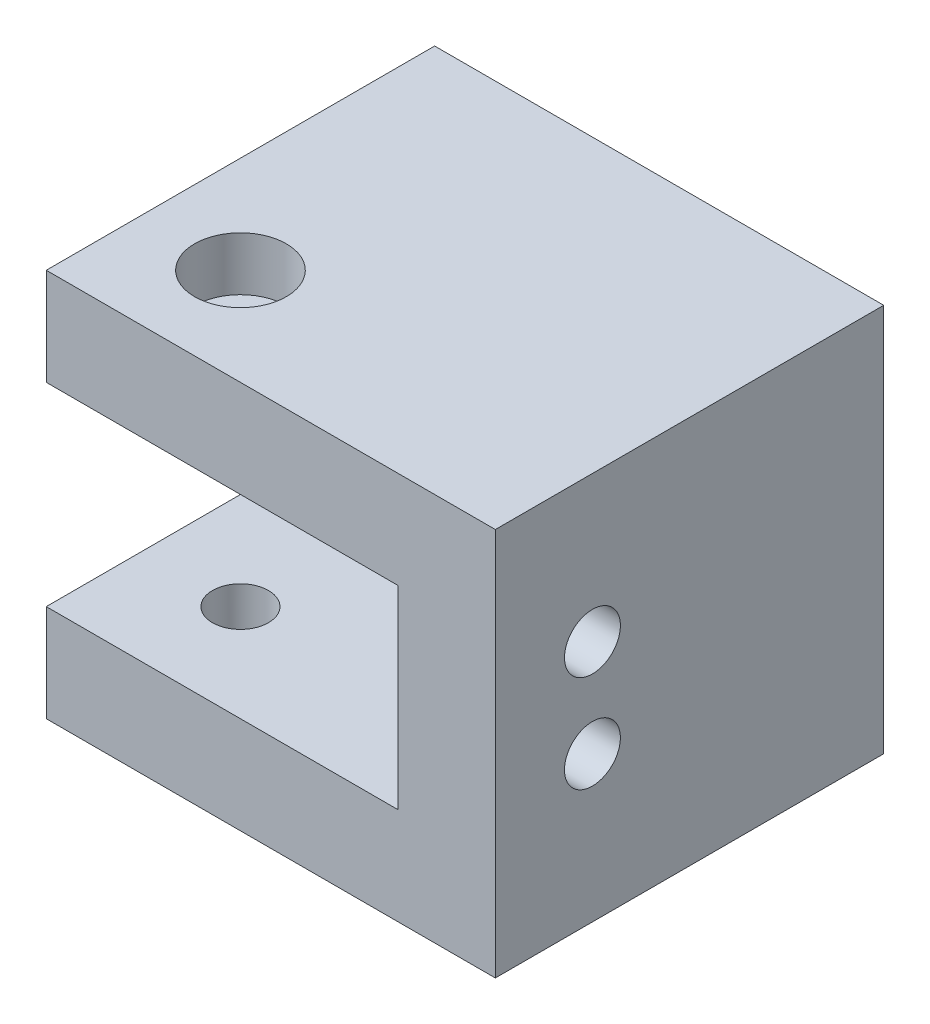
SolidWorks part; units mm, degrees
material "6061 Alloy"
ref_plane "Front Plane" through (0, 0, 0) normal (0, 0, 1) x (1, 0, 0)
ref_plane "Top Plane" through (0, 0, 0) normal (0, 1, 0) x (1, 0, 0)
ref_plane "Right Plane" through (0, 0, 0) normal (1, 0, 0) x (0, 0, -1)
sketch "Sketch1" plane through (0, 0, 0) normal (0, 0, 1) x (1, 0, 0)
  line L1 (0, 0) -> (29.3688, 0)
  line L2 (0, 0) -> (0, 25.4)
  line L3 (0, 25.4) -> (29.3687, 25.4)
  line L4 (29.3688, 0) -> (29.3687, 25.4)
  dimension "D1" = 29.3688
  dimension "D2" = 25.4
extrude "Boss-Extrude1" add sketch "Sketch1" along normal blind 25.4
sketch "Sketch2" plane through (0, 0, 25.4) normal (0, 0, 1) x (1, 0, 0)
  line L0 (0, 25.4) -> (0, 0) construction
  line L1 (0, 19.05) -> (23.0188, 19.05)
  line L2 (0, 19.05) -> (0, 6.35)
  line L3 (0, 6.35) -> (23.0188, 6.35)
  line L4 (23.0188, 19.05) -> (23.0188, 6.35)
  line L5 (29.3688, 0) -> (29.3688, 25.4) construction
  line L6 (29.3687, 25.4) -> (0, 25.4) construction
  line L7 (0, 0) -> (29.3688, 0) construction
  dimension "D1" = 6.35
  dimension "D2" = 6.35
  dimension "D3" = 6.35
extrude "Cut-Extrude1" cut sketch "Sketch2" against normal blind 15.875
hole_wizard "CBORE for #6 Socket Head Cap Screw1" positions "Sketch4" profile "Sketch5" counterbore size "#6" standard "ANSI Inch" end condition through all
sketch "Sketch4" plane through (0, 25.4, 0) normal (0, 1, 0) x (1, 0, 0)
  line L0 (0, -25.4) -> (0, 0) construction
  line L1 (29.3687, -25.4) -> (0, -25.4) construction
  point P0 (6.35, -19.05)
  dimension "D1" = 6.35
  dimension "D2" = 6.35
sketch "Sketch5" plane through (6.35, 25.4, 19.05) normal (1, 0, 0) x (0, 0, 1)
  line L0 (0, 0) -> (0, 25.4)
  line L1 (0, 25.4) -> (1.8288, 25.4)
  line L3 (1.8288, 25.4) -> (1.8288, 3.5052)
  line L4 (1.8288, 3.5052) -> (3, 3.5052)
  line L5 (3, 3.5052) -> (3, 0)
  line L7 (3, 0) -> (0, 0)
  line L11 (0, -6.35) -> (0, 107.95) construction
  dimension "Thru Hole Dia." = 3.6576
  dimension "Thru Hole Depth" = 25.4
  dimension "C'Bore Dia." = 6
  dimension "C'Bore Depth" = 3.5052
hole_wizard "#6 Clearance Hole2" positions "Sketch7" profile "Sketch6" hole size "#6" standard "ANSI Inch" end condition through all
sketch "Sketch7" plane through (29.3688, 0, 0) normal (1, 0, 0) x (0, 0, -1)
  line L0 (-25.4, 0) -> (-25.4, 25.4) construction
  line L1 (-25.4, 25.4) -> (0, 25.4) construction
  line L2 (-25.4, 0) -> (0, 0) construction
  point P0 (-19.05, 15.875)
  point P2 (-19.05, 9.525)
  dimension "D1" = 6.35
  dimension "D2" = 6.35
  dimension "D3" = 9.525
  dimension "D4" = 9.525
sketch "Sketch6" plane through (29.3688, 15.875, 19.05) normal (0, 1, 0) x (0, 0, -1)
  line L0 (0, 0) -> (0, 29.3688)
  line L1 (0, 29.3688) -> (1.8288, 29.3688)
  line L2 (1.8288, 29.3688) -> (1.8288, 0)
  line L5 (1.8288, 0) -> (0, 0)
  line L11 (0, -6.35) -> (0, 107.95) construction
  dimension "Thru Hole Dia." = 3.6576
  dimension "Thru Hole Depth" = 29.3688
fillet "Fillet1" radius 3.175 2 edges at (11.5094, 6.35, 9.525) (11.5094, 19.05, 9.525)
hole_wizard "Tap Drill for 1/4-20 Tap2" positions "Sketch9" profile "Sketch8" hole size "1/4-20" standard "ANSI Inch" end condition through all
sketch "Sketch9" plane through (0, 0, 9.525) normal (0, 0, 1) x (1, 0, 0)
  line L0 (0, 15.875) -> (0, 9.525) construction
  line L2 (29.3687, 25.4) -> (0, 25.4) construction
  line L3 (0, 0) -> (29.3688, 0) construction
  point P0 (6.35, 12.7)
  point P2 (17.78, 12.7)
  dimension "D1" = 6.35
  dimension "D2" = 17.78
  dimension "D3" = 12.7
  dimension "D4" = 12.7
sketch "Sketch8" plane through (6.35, 12.7, 9.525) normal (1, 0, 0) x (0, -1, 0)
  line L0 (0, 0) -> (0, 9.525)
  line L1 (0, 9.525) -> (2.5527, 9.525)
  line L2 (2.5527, 9.525) -> (2.5527, 0)
  line L5 (2.5527, 0) -> (0, 0)
  line L11 (0, -6.35) -> (0, 107.95) construction
  dimension "Thru Hole Dia." = 5.1054
  dimension "Thru Hole Depth" = 9.525
